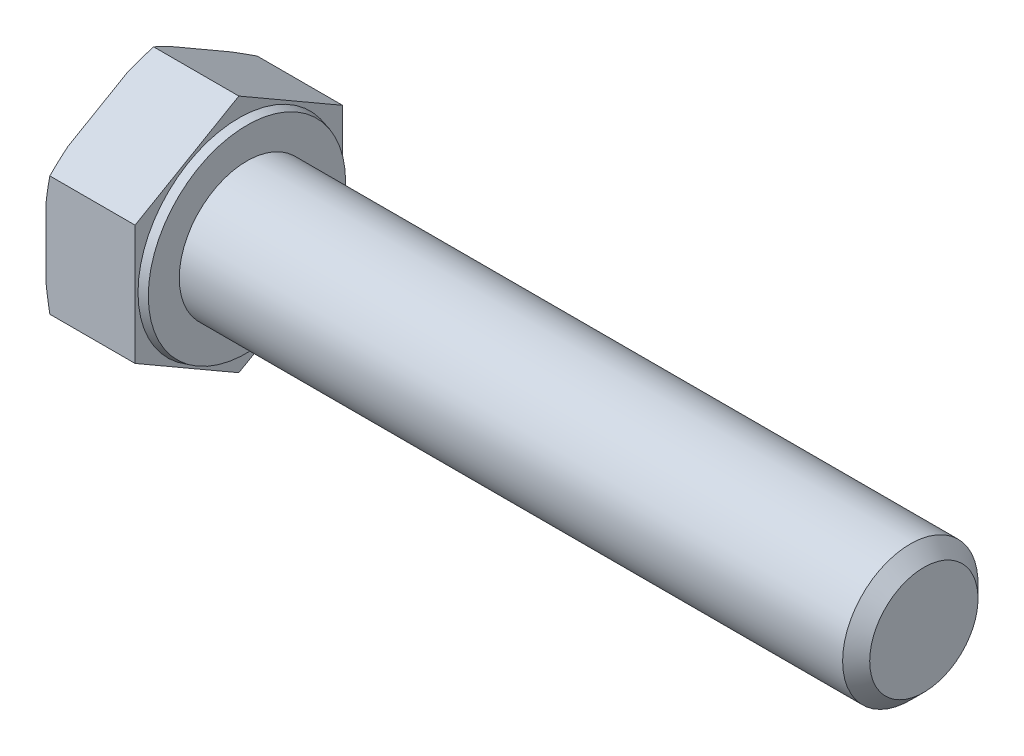
SolidWorks part; units mm, degrees
material "AISI 1020"
ref_plane "Спереди" through (0, 0, 0) normal (0, 0, 1) x (1, 0, 0)
ref_plane "Сверху" through (0, 0, 0) normal (0, 1, 0) x (1, 0, 0)
ref_plane "Справа" through (0, 0, 0) normal (1, 0, 0) x (0, 0, -1)
sketch "Эскиз1" plane through (0, 0, 0) normal (0, 0, 1) x (1, 0, 0)
  line L0 (-1000, 0) -> (49000, 0) construction
  line L1 (-6.58, 0) -> (-6.58, 8.85)
  line L2 (-6.58, 8.85) -> (0, 8.85)
  line L3 (0, 8.85) -> (0, 7.449)
  line L4 (0.6, 5) -> (50.6, 5)
  line L5 (50.6, 5) -> (50.6, 0)
  line L6 (-6.58, 0) -> (50.6, 0)
  line L7 (0, 7.449) -> (0.6, 7.2882)
  line L8 (0.6, 7.2882) -> (0.6, 5)
  line L9 (0.5, 0) -> (0.5, 7.315) construction
  dimension "_d" = 10
  dimension "D1" = 50
  dimension "D5" = 17.7
  dimension "D2" = 0.6
  dimension "D3" = 6.58
  dimension "D4" = 0.1
  dimension "D6" = 14.63
  dimension "D7" = 75
revolve "Повернуть1" add sketch "Эскиз1" angle 360 about L0
sketch "Эскиз2" plane through (-6.58, 0, 0) normal (-1, 0, 0) x (0, 0, 1)
  line L1 (0, -8.85) -> (7.6643, -4.425)
  line L2 (7.6643, -4.425) -> (7.6643, 4.425)
  line L3 (7.6643, 4.425) -> (0, 8.85)
  line L4 (0, 8.85) -> (-7.6643, 4.425)
  line L5 (-7.6643, 4.425) -> (-7.6643, -4.425)
  line L6 (-7.6643, -4.425) -> (0, -8.85)
  circle A0 centre (0, 0) radius 7.6643 construction
  circle A1 centre (0, 0) radius 8.85 construction
extrude "Вырез-Вытянуть1" cut sketch "Эскиз2" against normal through all flip side to cut
sketch "Эскиз4" plane through (0, 0, 0) normal (0, 0, 1) x (1, 0, 0)
  line L0 (-1000, 0) -> (49000, 0) construction
  line L1 (-6.58, 8.075) -> (-6.2979, 8.85)
  line L2 (-6.2979, 8.85) -> (-6.58, 8.85)
  line L3 (-6.58, 8.85) -> (-6.58, 8.075)
  line L4 (-6.58, 4.425) -> (-6.58, 8.85) construction
  line L6 (0, 8.85) -> (-6.58, 8.85) construction
  dimension "D1" = 20
  dimension "D2" = 16.15
revolve "Вырез-Повернуть1" cut sketch "Эскиз4" angle 360 about L0
chamfer "Фаска1" distance 1 angle 45 1 edges at (50.6, 0, 5)
equation "\"l\"= 50'длина болта"
equation "\"_d\"= 10'диаметр болта"
equation "\"b\"= 20'длина резьбы"
equation "\"k\"= 6.58'толщина шляпки"
equation "\"e\"= 17.7'диаметр головки описанный"
equation "\"S\"= 17'размер под ключ"
equation "\"_d@Эскиз1\"=\"_d\""
equation "\"dw\"= 14.63"
equation "\"da\"= 9.78"
equation "\"с\"= 0.6"
equation "\"D1@Эскиз1\"=\"l\""
equation "\"D5@Эскиз1\"=\"e\""
equation "\"D2@Эскиз1\"=\"с\""
equation "\"D3@Эскиз1\"=\"k\""
equation "\"D2@Эскиз4\"=\"S\"*0.95"
equation "\"D1@Фаска1\"=\"_d\"/10"
equation "\"D6@Эскиз1\"=\"dw\""
